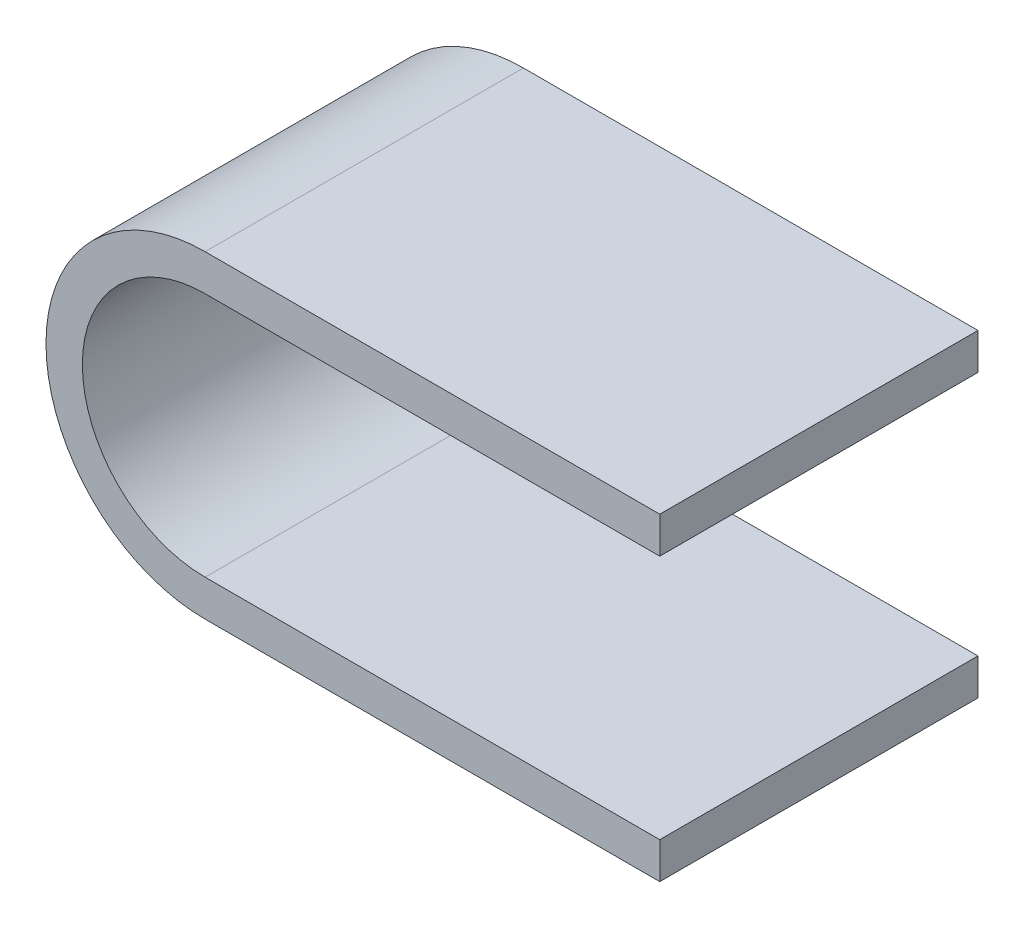
SolidWorks part; units mm, degrees
ref_plane "Plan de face" through (0, 0, 0) normal (0, 0, 1) x (1, 0, 0)
ref_plane "Plan de dessus" through (0, 0, 0) normal (0, 1, 0) x (1, 0, 0)
ref_plane "Plan de droite" through (0, 0, 0) normal (1, 0, 0) x (0, 0, -1)
sketch "Esquisse2" plane through (0, 0, 0) normal (0, 0, 1) x (1, 0, 0)
  line L0 (0, 0) -> (-50, 0)
  line L1 (-50, 35) -> (0, 35)
  line L2 (0, 4) -> (-50, 4)
  line L3 (-50, 31) -> (0, 31)
  line L4 (0, 35) -> (0, 31)
  line L5 (0, 4) -> (0, 0)
  arc A0 (-50, 0) -> (-50, 35) centre (-50, 17.5) cw
  arc A1 (-50, 4) -> (-50, 31) centre (-50, 17.5) cw
  point P11 (-71.3371, 25.6647)
  point P12 (-80.1184, 29.7948)
  point P13 (0, 0)
  dimension "D3" = 13.5
  dimension "D1" = 50
  dimension "D4" = 50
  dimension "D2" = 4
extrude "Boss.-Extru.1" add sketch "Esquisse2" along normal blind 35
